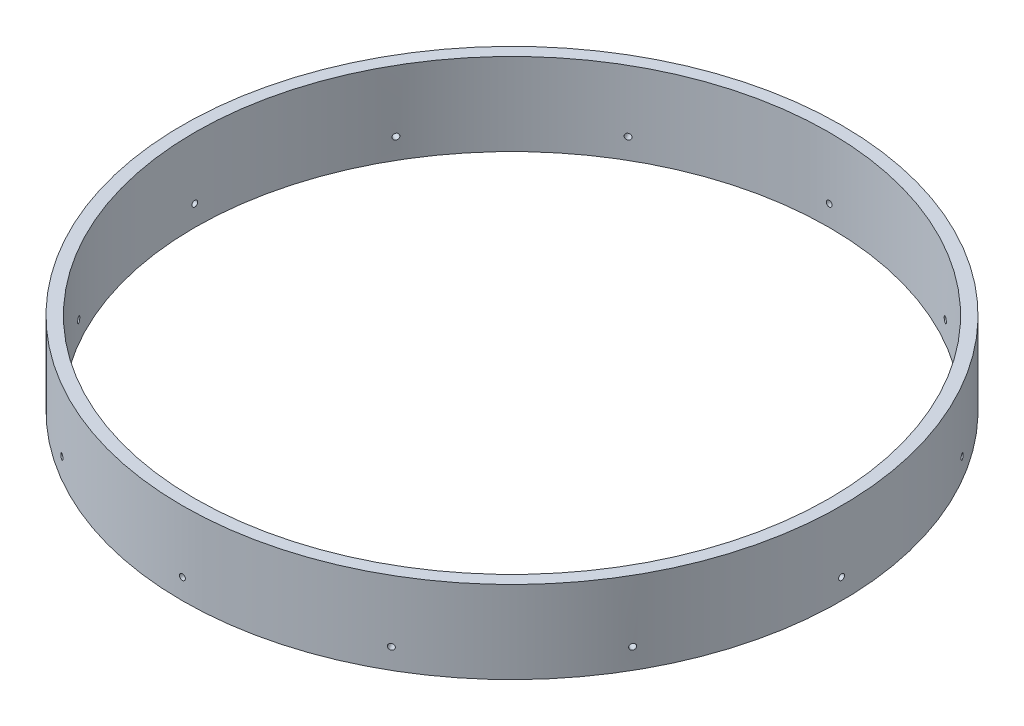
SolidWorks part; units mm, degrees
ref_plane "Front Plane" through (0, 0, 0) normal (0, 0, 1) x (1, 0, 0)
ref_plane "Top Plane" through (0, 0, 0) normal (0, 1, 0) x (1, 0, 0)
ref_plane "Right Plane" through (0, 0, 0) normal (1, 0, 0) x (0, 0, -1)
sketch "Sketch1" plane through (0, 0, 0) normal (0, 1, 0) x (1, 0, 0)
  circle A0 centre (0, 0) radius 101.6
  circle A1 centre (0, 0) radius 82.55
  dimension "D1" = 203.2
  dimension "D2" = 165.1
extrude "Boss-Extrude1" add sketch "Sketch1" along normal blind 25.4
sketch "Sketch2" plane through (0, 25.4, 0) normal (0, 1, 0) x (1, 0, 0)
  circle A0 centre (0, 0) radius 63.5
  circle A1 centre (0, 0) radius 97.79
  dimension "D1" = 195.58
  dimension "D2" = 127
extrude "Cut-Extrude1" cut sketch "Sketch2" against normal blind 50.8
sketch "Sketch3" plane through (0, 0, 0) normal (0, 0, 1) x (1, 0, 0)
  circle A0 centre (0, 6.35) radius 0.9
  dimension "D1" = 1.8
  dimension "D2" = 6.35
extrude "Cut-Extrude2" cut sketch "Sketch3" against normal blind 254
pattern_circular "CirPattern1" count 12 over 360 about axis through (0, 25.4, 0) along (0, 1, 0) of "Cut-Extrude2"
